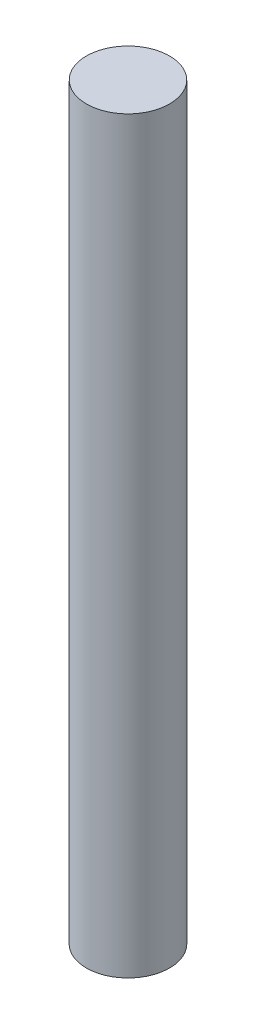
SolidWorks part; units mm, degrees
ref_plane "Front Plane" through (0, 0, 0) normal (0, 0, 1) x (1, 0, 0)
ref_plane "Top Plane" through (0, 0, 0) normal (0, 1, 0) x (1, 0, 0)
ref_plane "Right Plane" through (0, 0, 0) normal (1, 0, 0) x (0, 0, -1)
sketch "Sketch1" plane through (0, 0, 0) normal (0, 1, 0) x (1, 0, 0)
  circle A0 centre (0, 0) radius 2
  dimension "D1" = 4
extrude "Boss-Extrude1" add sketch "Sketch1" along normal mid plane 36
